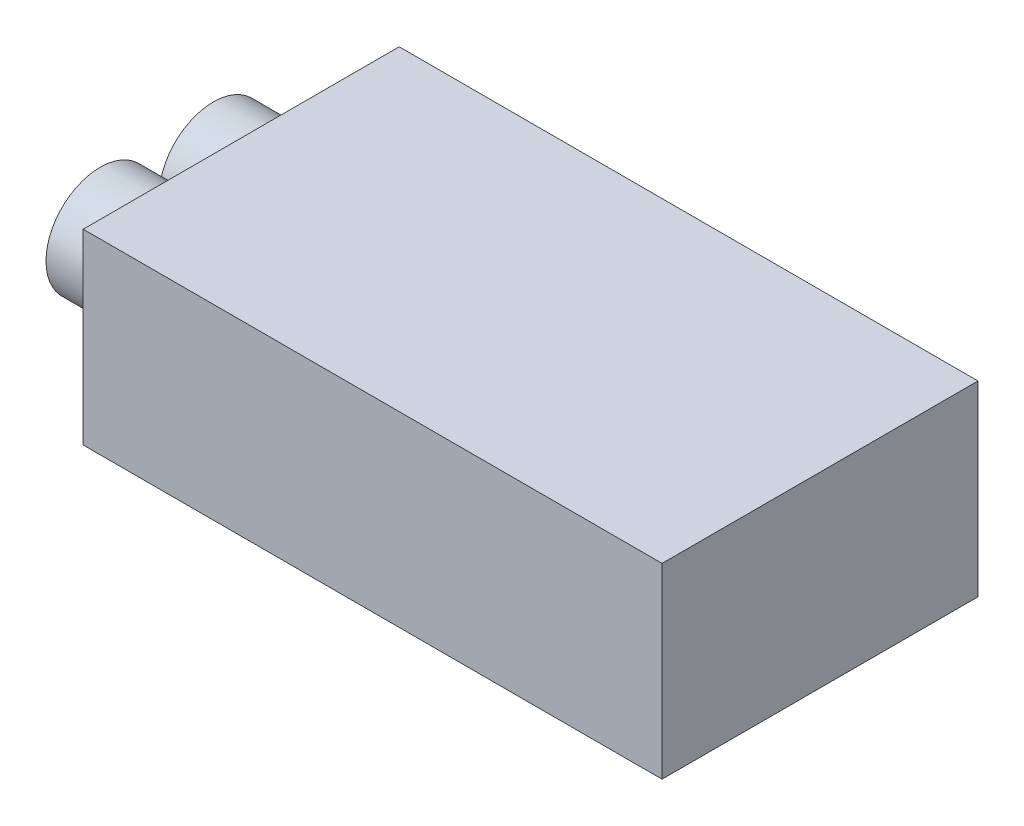
SolidWorks part; units mm, degrees
ref_plane "Front Plane" through (0, 0, 0) normal (0, 0, 1) x (1, 0, 0)
ref_plane "Top Plane" through (0, 0, 0) normal (0, 1, 0) x (1, 0, 0)
ref_plane "Right Plane" through (0, 0, 0) normal (1, 0, 0) x (0, 0, -1)
sketch "Sketch1" plane through (0, 0, 0) normal (0, 1, 0) x (1, 0, 0)
  line L0 (0, 0) -> (48, 0)
  line L1 (48, 0) -> (48, 26.2012)
  line L2 (48, 26.2012) -> (0, 26.2012)
  line L3 (0, 26.2012) -> (0, 0)
extrude "Boss-Extrude1" add sketch "Sketch1" along normal blind 15.5
ref_plane "Plane1" through (0, 0, 0) normal (-1, 0, 0) x (0, 0, 1)
sketch "Sketch2" plane through (0, 0, 0) normal (-1, 0, 0) x (0, 0, 1)
  line L0 (-26.2012, 7.75) -> (0, 7.75)
  line L1 (-26.2012, 15.5) -> (-26.2012, 0) construction
  line L2 (0, 15.5) -> (0, 0) construction
  line L3 (-13.1006, 15.5) -> (-13.1006, 0)
  line L4 (-26.2012, 15.5) -> (0, 15.5) construction
  line L5 (-26.2012, 0) -> (0, 0) construction
  circle A0 centre (-17.79, 7.75) radius 4.498
  circle A1 centre (-8.4112, 7.75) radius 4.498
extrude "Boss-Extrude2" add sketch "Sketch2" along normal blind 7 separate body contours L0 A0 | L0 A0 | A1 L0 | A1 L0
